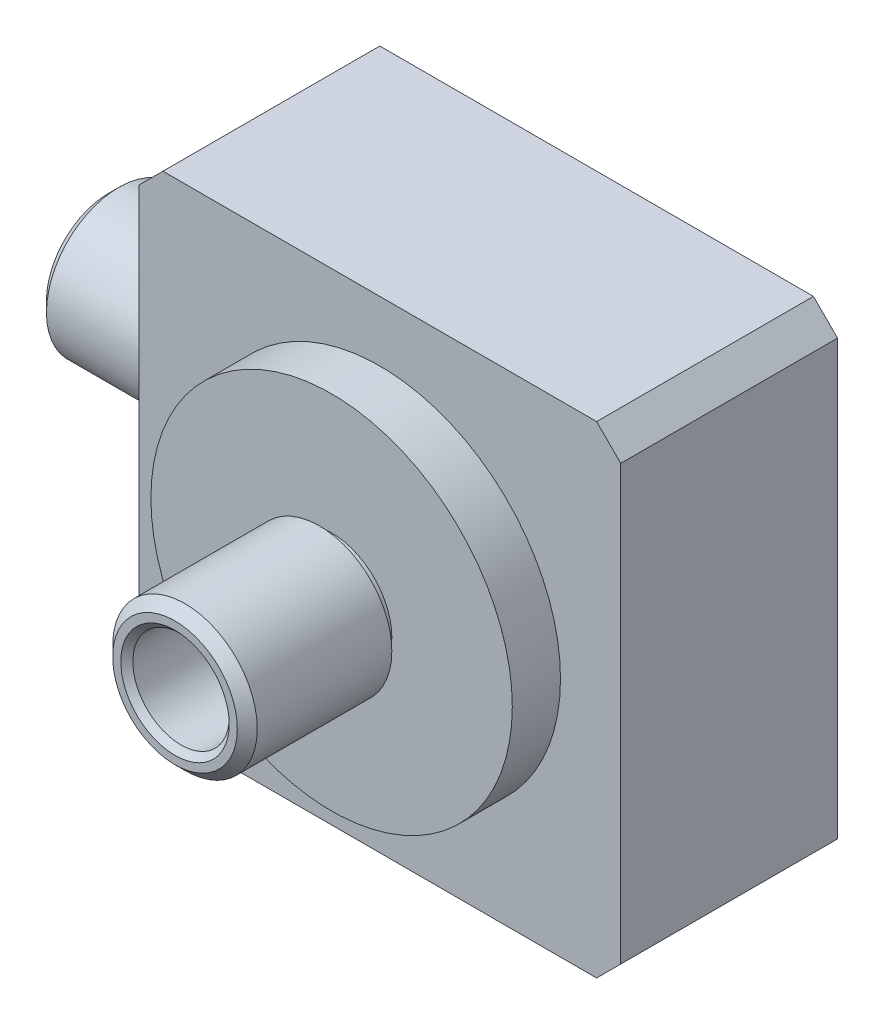
SolidWorks part; units mm, degrees
material "Тефлон"
ref_plane "Спереди" through (0, 0, 0) normal (0, 0, 1) x (1, 0, 0)
ref_plane "Сверху" through (0, 0, 0) normal (0, 1, 0) x (1, 0, 0)
ref_plane "Справа" through (0, 0, 0) normal (1, 0, 0) x (0, 0, -1)
sketch "Эскиз1" plane through (0, 0, 0) normal (0, 0, 1) x (1, 0, 0)
  line L1 (-20, -20) -> (20, -20)
  line L2 (-20, -20) -> (-20, 20)
  line L3 (-20, 20) -> (20, 20)
  line L4 (20, -20) -> (20, 20)
  line L5 (-20, -20) -> (20, 20) construction
  line L6 (-20, 20) -> (20, -20) construction
  point P0 (0, 0)
  dimension "D1" = 40
extrude "Бобышка-Вытянуть1" add sketch "Эскиз1" along normal blind 18
sketch "Эскиз2" plane through (0, 0, 18) normal (0, 0, 1) x (1, 0, 0)
  circle A0 centre (0, 0) radius 15
  dimension "D1" = 30
extrude "Бобышка-Вытянуть2" add sketch "Эскиз2" along normal blind 4
sketch "Эскиз3" plane through (0, 0, 22) normal (0, 0, 1) x (1, 0, 0)
  circle A0 centre (0, 0) radius 5
  dimension "D1" = 10
extrude "Бобышка-Вытянуть3" add sketch "Эскиз3" along normal blind 1
sketch "Эскиз4" plane through (0, 0, 23) normal (0, 0, 1) x (1, 0, 0)
  circle A0 centre (0, 0) radius 6
  dimension "D1" = 12
extrude "Бобышка-Вытянуть4" add sketch "Эскиз4" along normal blind 12
cosmetic thread "Условное изображение резьбы1" parameters "D2"=10.344
sketch "Эскиз5" plane through (-20, 0, 0) normal (-1, 0, 0) x (0, 0, 1)
  line L0 (0, 0) -> (18, 0) construction
  line L1 (18, 20) -> (18, -20) construction
  circle A0 centre (7, 0) radius 5
  dimension "D1" = 10
  dimension "D2" = 11
extrude "Бобышка-Вытянуть5" add sketch "Эскиз5" along normal blind 1
sketch "Эскиз6" plane through (-21, 0, 0) normal (-1, 0, 0) x (0, 0, 1)
  circle A0 centre (7, 0) radius 6
  dimension "D1" = 12
extrude "Бобышка-Вытянуть6" add sketch "Эскиз6" along normal blind 12.5
cosmetic thread "Условное изображение резьбы2" parameters "D2"=10.344
sketch "Эскиз7" plane through (0, 0, 0) normal (0, 1, 0) x (1, 0, 0)
  line L0 (0, 0) -> (0, -8)
  line L1 (0, -8) -> (3.5, -8)
  line L2 (3.5, -8) -> (8.6962, -11)
  line L3 (8.6962, -11) -> (11, -11)
  line L4 (11, -11) -> (11, 0)
  line L5 (20, 0) -> (-20, 0) construction
  line L6 (11, 0) -> (0, 0)
  dimension "D1" = 8
  dimension "D2" = 3.5
  dimension "D3" = 30
  dimension "D4" = 11
  dimension "D5" = 11
revolve "Вырез-Повернуть1" cut sketch "Эскиз7" angle 360 about L0
sketch "Эскиз8" plane through (0, 0, 35) normal (0, 0, 1) x (1, 0, 0)
  circle A0 centre (0, 0) radius 2.5
  dimension "D1" = 5
extrude "Вырез-Вытянуть1" cut sketch "Эскиз8" against normal through all
sketch "Эскиз9" plane through (0, 0, 35) normal (0, 0, 1) x (1, 0, 0)
  circle A0 centre (0, 0) radius 4
  dimension "D1" = 8
extrude "Вырез-Вытянуть2" cut sketch "Эскиз9" against normal blind 10
sketch "Эскиз10" plane through (-33.5, 0, 0) normal (-1, 0, 0) x (0, 0, 1)
  circle A0 centre (7, 0) radius 2.5
  dimension "D1" = 5
extrude "Вырез-Вытянуть3" cut sketch "Эскиз10" against normal up to next
sketch "Эскиз11" plane through (-33.5, 0, 0) normal (-1, 0, 0) x (0, 0, 1)
  circle A0 centre (7, 0) radius 4
  dimension "D1" = 8
extrude "Вырез-Вытянуть4" cut sketch "Эскиз11" against normal blind 10
chamfer "Фаска1" distance 0.5 angle 45 2 edges at (4, 0, 35) (-33.5, 0, 11)
chamfer "Фаска2" distance 0.828 angle 45 2 edges at (6, 0, 35) (-33.5, 0, 13)
chamfer "Фаска3" distance 2 angle 45 4 edges at (-20, 20, 9) (20, 20, 9) (20, -20, 9) (-20, -20, 9)
sketch "Эскиз12" plane through (0, 0, 0) normal (0, 1, 0) x (1, 0, 0)
  line L0 (15.5, 0) -> (15.5, 3) construction
  line L1 (13.5, 0) -> (13.5, 3)
  line L2 (17.5, 0) -> (17.5, 3)
  line L3 (0, 0) -> (0, -11.7318) construction
  arc A0 (13.5, 0) -> (17.5, 0) centre (15.5, 0) ccw
  arc A1 (17.5, 3) -> (13.5, 3) centre (15.5, 3) ccw
  point P2 (15.5, 1.5)
  dimension "D3" = 2
  dimension "D1" = 15.5
  dimension "D2" = 3
  dimension "D4" = 1.5
revolve "Вырез-Повернуть2" cut sketch "Эскиз12" angle 360 about L3
